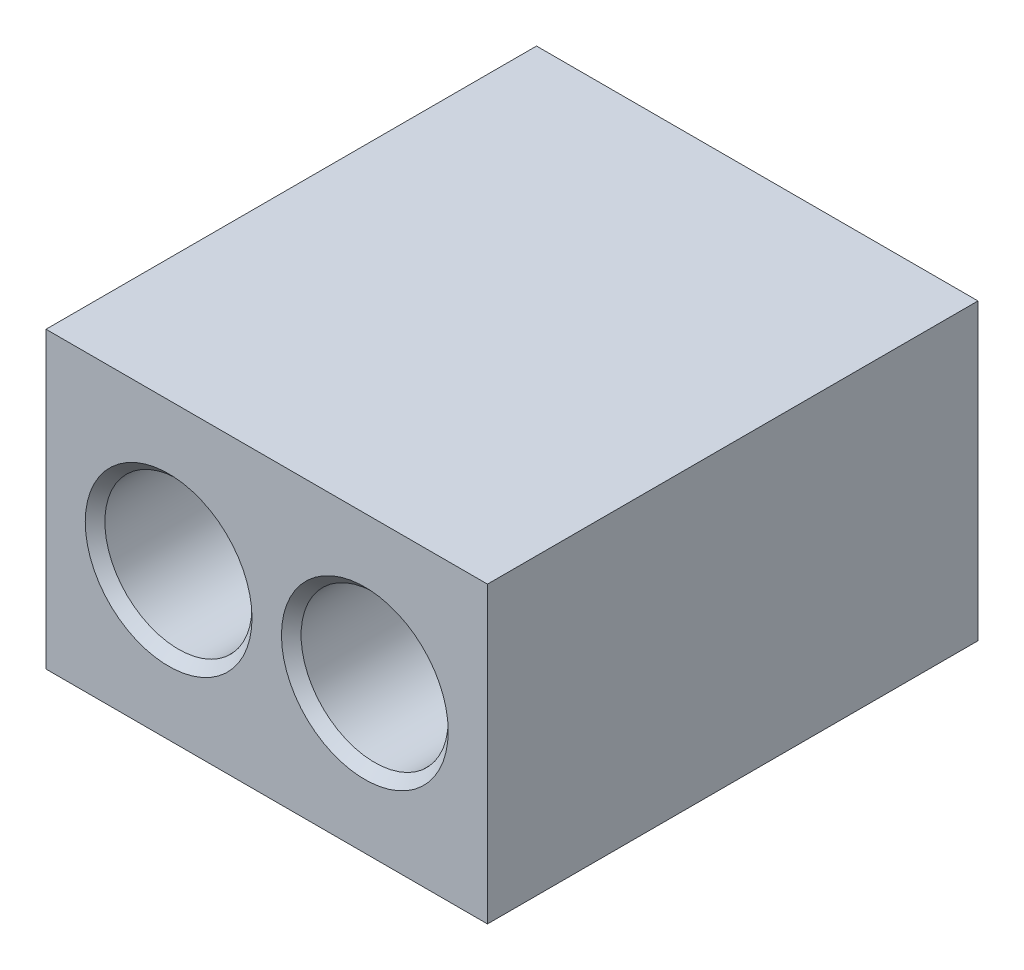
SolidWorks part; units mm, degrees
ref_plane "Front Plane" through (0, 0, 0) normal (0, 0, 1) x (1, 0, 0)
ref_plane "Top Plane" through (0, 0, 0) normal (0, 1, 0) x (1, 0, 0)
ref_plane "Right Plane" through (0, 0, 0) normal (1, 0, 0) x (0, 0, -1)
sketch "Sketch1" plane through (0, 0, 0) normal (0, 0, 1) x (1, 0, 0)
  line L1 (-22.5, 15) -> (22.5, 15)
  line L2 (-22.5, 15) -> (-22.5, -15)
  line L3 (-22.5, -15) -> (22.5, -15)
  line L4 (22.5, 15) -> (22.5, -15)
  line L5 (-22.5, 15) -> (22.5, -15) construction
  line L6 (-22.5, -15) -> (22.5, 15) construction
  circle A0 centre (-10, 0) radius 7.5
  circle A1 centre (10, 0) radius 7.5
  point P0 (0, 0)
  point P10 (0, 0)
  dimension "D1" = 15
  dimension "D2" = 10
  dimension "D3" = 10
  dimension "D4" = 45
  dimension "D5" = 30
extrude "Boss-Extrude1" add sketch "Sketch1" along normal mid plane 50
chamfer "Chamfer1" distance 1 angle 45 4 edges at (-2.5, 0, -25) (17.5, 0, -25) (-2.5, 0, 25) (17.5, 0, 25)
